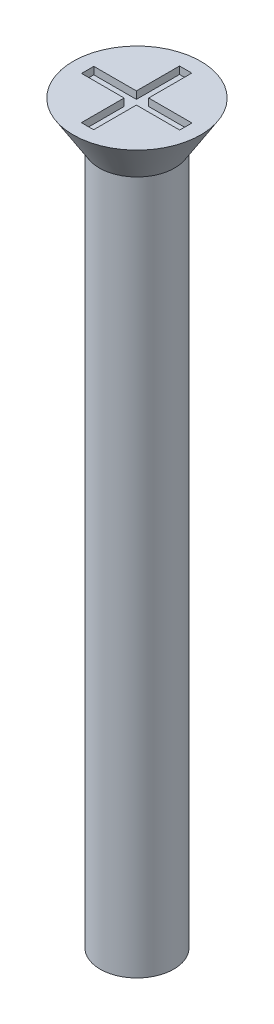
SolidWorks part; units mm, degrees
material "AISI 304"
ref_plane "Front" through (0, 0, 0) normal (0, 0, 1) x (1, 0, 0)
ref_plane "Top" through (0, 0, 0) normal (0, 1, 0) x (1, 0, 0)
ref_plane "Right" through (0, 0, 0) normal (1, 0, 0) x (0, 0, -1)
sketch "Sketch1" plane through (0, 0, 0) normal (0, 1, 0) x (1, 0, 0)
  circle A0 centre (0, 0) radius 1.5
  dimension "D1" = 3
extrude "Boss-Extrude1" add sketch "Sketch1" along normal blind 30
sketch "Sketch2" plane through (0, 30, 0) normal (0, 1, 0) x (1, 0, 0)
  circle A0 centre (0, 0) radius 2.6
  dimension "D1" = 5.2
extrude "Boss-Extrude2" add sketch "Sketch2" against normal blind 1.7 draft 32
sketch "Sketch3" plane through (0, 30, 0) normal (0, 1, 0) x (1, 0, 0)
  line L1 (-2, 0.2416) -> (2, 0.2416)
  line L2 (-2, 0.2416) -> (-2, -0.2584)
  line L3 (-2, -0.2584) -> (2, -0.2584)
  line L4 (2, 0.2416) -> (2, -0.2584)
  line L5 (-0.2653, 2) -> (0.2347, 2)
  line L6 (-0.2653, 2) -> (-0.2653, -2)
  line L7 (-0.2653, -2) -> (0.2347, -2)
  line L8 (0.2347, 2) -> (0.2347, -2)
  circle A0 centre (0, 0) radius 2.6 construction
  dimension "D1" = 0.5
  dimension "D2" = 0.5
  dimension "D3" = 4
  dimension "D4" = 4
  dimension "D5" = 2
  dimension "D6" = 2
extrude "Cut-Extrude1" cut sketch "Sketch3" against normal blind 0.3 contours L8 L5 L6 L1 | L8 L3 L6 L7 | L6 L1 L2 L3 | L1 L8 L3 L4 | L8 L1 L6 L3
